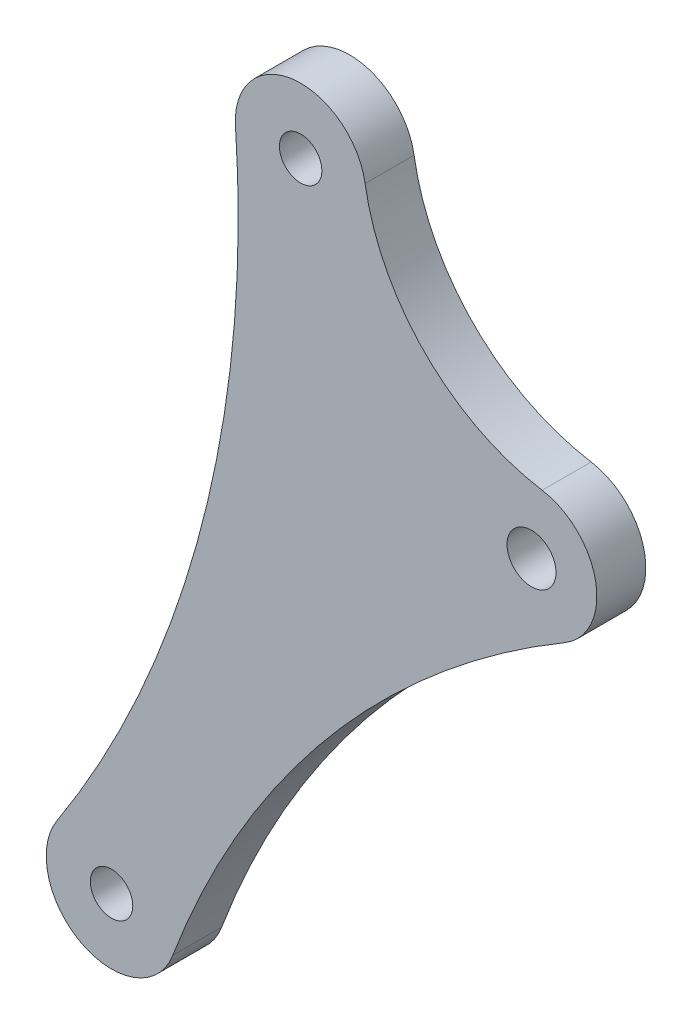
SolidWorks part; units mm, degrees
ref_plane "Front Plane" through (0, 0, 0) normal (0, 0, 1) x (1, 0, 0)
ref_plane "Top Plane" through (0, 0, 0) normal (0, 1, 0) x (1, 0, 0)
ref_plane "Right Plane" through (0, 0, 0) normal (1, 0, 0) x (0, 0, -1)
sketch "Model" plane through (0, 0, 0) normal (0, 0, 1) x (1, 0, 0)
  circle A0 centre (42.3849, 15.7273) radius 1.3
  circle A1 centre (53.966, 60.5081) radius 1.3
  circle A2 centre (68.1046, 46.3624) radius 1.5
  arc A3 (57.9133, 61.1561) -> (49.9759, 60.2288) centre (53.9662, 60.5075) ccw
  arc A4 (57.9133, 61.1561) -> (68.7545, 50.3092) centre (70.8913, 63.286) ccw
  arc A5 (70.1377, 42.9176) -> (68.7545, 50.3092) centre (68.1044, 46.3623) ccw
  arc A6 (39.0302, 17.9058) -> (49.9759, 60.2288) centre (-18.7455, 55.4248) ccw
  arc A7 (39.0302, 17.9058) -> (46.1297, 14.3213) centre (42.3849, 15.7273) ccw
  arc A8 (70.1377, 42.9176) -> (46.1297, 14.3213) centre (98.6579, -5.4027) ccw
extrude "Boss-Extrude1" add sketch "Model" along normal blind 3
